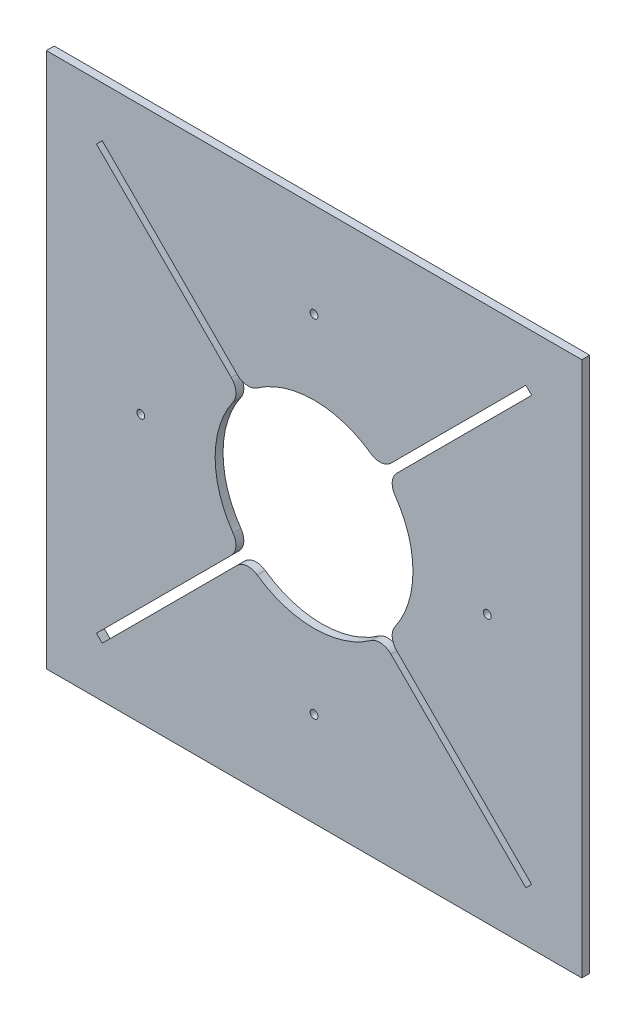
SolidWorks part; units mm, degrees
ref_plane "Front Plane" through (0, 0, 0) normal (0, 0, 1) x (1, 0, 0)
ref_plane "Top Plane" through (0, 0, 0) normal (0, 1, 0) x (1, 0, 0)
ref_plane "Right Plane" through (0, 0, 0) normal (1, 0, 0) x (0, 0, -1)
sketch "Sketch1" plane through (0, 0, 0) normal (0, 0, 1) x (1, 0, 0)
  line L1 (-215.9, 215.9) -> (215.9, 215.9)
  line L2 (-215.9, 215.9) -> (-215.9, -215.9)
  line L3 (-215.9, -215.9) -> (215.9, -215.9)
  line L4 (215.9, 215.9) -> (215.9, -215.9)
  line L5 (-215.9, 215.9) -> (215.9, -215.9) construction
  line L6 (-215.9, -215.9) -> (215.9, 215.9) construction
  point P0 (0, 0)
  dimension "D1" = 431.8
extrude "Boss-Extrude1" add sketch "Sketch1" along normal blind 6.35
sketch "Sketch2" plane through (0, 0, 6.35) normal (0, 0, 1) x (1, 0, 0)
  circle A0 centre (0, 0) radius 79.756
  dimension "D1" = 159.512
extrude "Cut-Extrude1" cut sketch "Sketch2" against normal blind 6.35
sketch "Sketch3" plane through (0, 0, 6.35) normal (0, 0, 1) x (1, 0, 0)
  line L0 (0, 0) -> (-215.9, 215.9) construction
  line L3 (-170.8045, 175.4742) -> (-175.4742, 170.8045)
  line L5 (62.6822, -58.0125) -> (-175.4742, 170.8045) construction
  line L6 (-170.8045, 175.4742) -> (58.0125, -62.6822) construction
  line L7 (-55.5322, 50.8625) -> (-50.8625, 55.5322)
  line L8 (-55.5322, 50.8625) -> (58.0125, -62.6822) construction
  line L9 (58.0125, -62.6822) -> (62.6822, -58.0125) construction
  line L10 (62.6822, -58.0125) -> (-50.8625, 55.5322) construction
  line L11 (-55.5322, 50.8625) -> (-175.4742, 170.8045)
  line L12 (-170.8045, 175.4742) -> (-50.8625, 55.5322)
  line L13 (175.4742, 170.8045) -> (170.8045, 175.4742)
  line L14 (50.8625, 55.5322) -> (55.5322, 50.8625)
  line L15 (50.8625, 55.5322) -> (170.8045, 175.4742)
  line L16 (175.4742, 170.8045) -> (55.5322, 50.8625)
  line L17 (-58.0125, -62.6822) -> (170.8045, 175.4742) construction
  line L18 (175.4742, 170.8045) -> (-62.6822, -58.0125) construction
  line L19 (50.8625, 55.5322) -> (-62.6822, -58.0125) construction
  line L20 (-62.6822, -58.0125) -> (-58.0125, -62.6822) construction
  line L21 (-58.0125, -62.6822) -> (55.5322, 50.8625) construction
  line L22 (170.8045, -175.4742) -> (175.4742, -170.8045)
  line L23 (55.5322, -50.8625) -> (50.8625, -55.5322)
  line L24 (55.5322, -50.8625) -> (175.4742, -170.8045)
  line L25 (170.8045, -175.4742) -> (50.8625, -55.5322)
  line L26 (-62.6822, 58.0125) -> (175.4742, -170.8045) construction
  line L27 (170.8045, -175.4742) -> (-58.0125, 62.6822) construction
  line L28 (55.5322, -50.8625) -> (-58.0125, 62.6822) construction
  line L29 (-58.0125, 62.6822) -> (-62.6822, 58.0125) construction
  line L30 (-62.6822, 58.0125) -> (50.8625, -55.5322) construction
  line L31 (-175.4742, -170.8045) -> (-170.8045, -175.4742)
  line L32 (-50.8625, -55.5322) -> (-55.5322, -50.8625)
  line L33 (-50.8625, -55.5322) -> (-170.8045, -175.4742)
  line L34 (-175.4742, -170.8045) -> (-55.5322, -50.8625)
  line L35 (58.0125, 62.6822) -> (-170.8045, -175.4742) construction
  line L36 (-175.4742, -170.8045) -> (62.6822, 58.0125) construction
  line L37 (-50.8625, -55.5322) -> (62.6822, 58.0125) construction
  line L38 (62.6822, 58.0125) -> (58.0125, 62.6822) construction
  line L39 (58.0125, 62.6822) -> (-55.5322, -50.8625) construction
  point P4 (-56.396, 56.396)
  point P5 (-56.396, 56.396)
  point P14 (56.396, 56.396)
  point P15 (56.396, 56.396)
  point P22 (56.396, -56.396)
  point P23 (56.396, -56.396)
  point P30 (-56.396, -56.396)
  point P31 (-56.396, -56.396)
  point P38 (0, 0)
  dimension "D1" = 6.604
  dimension "D2" = 165.1
  dimension "D3" = 79.756
  dimension "D4" = 4
extrude "Cut-Extrude2" cut sketch "Sketch3" against normal blind 6.35
fillet "Fillet1" radius 12.7 8 edges at (58.6825, -54.0128, 3.175) (54.0128, -58.6825, 3.175) (-54.0128, -58.6825, 3.175) (-58.6825, -54.0128, 3.175) (58.6825, 54.0128, 3.175) (54.0128, 58.6825, 3.175) (-58.6825, 54.0128, 3.175) (-54.0128, 58.6825, 3.175)
sketch "Sketch4" plane through (0, 0, 6.35) normal (0, 0, 1) x (1, 0, 0)
  line L0 (0, 0) -> (0, 215.9) construction
  line L1 (215.9, 215.9) -> (-215.9, 215.9) construction
  line L2 (0, 0) -> (215.9, 0) construction
  line L3 (215.9, -215.9) -> (215.9, 215.9) construction
  circle A0 centre (0, 139.7) radius 3.175
  circle A1 centre (139.7, 0) radius 3.175
  circle A2 centre (0, -139.7) radius 3.175
  circle A3 centre (-139.7, 0) radius 3.175
  point P19 (0, 0)
  dimension "D1" = 6.35
  dimension "D2" = 76.2
  dimension "D3" = 4
extrude "Cut-Extrude3" cut sketch "Sketch4" against normal blind 6.35
